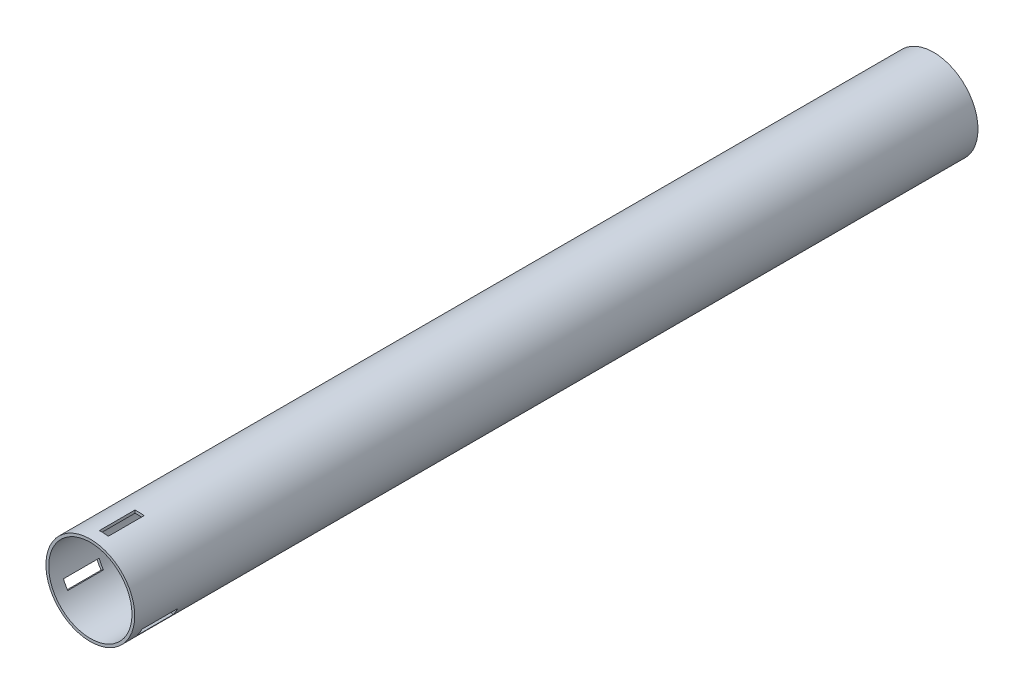
SolidWorks part; units mm, degrees
ref_plane "Front Plane" through (0, 0, 0) normal (0, 0, 1) x (1, 0, 0)
ref_plane "Top Plane" through (0, 0, 0) normal (0, 1, 0) x (1, 0, 0)
ref_plane "Right Plane" through (0, 0, 0) normal (1, 0, 0) x (0, 0, -1)
sketch "Sketch1" plane through (0, 0, 0) normal (0, 0, 1) x (1, 0, 0)
  circle A0 centre (0, 0) radius 23.6982
  circle A1 centre (0, 0) radius 22.225
extrude "Boss-Extrude1" add sketch "Sketch1" along normal blind 450
ref_plane "Plane1" through (0, 50.8, 0) normal (0, 1, 0) x (1, 0, 0)
sketch "Sketch3" plane through (0, 50.8, 0) normal (0, 1, 0) x (1, 0, 0)
  line L0 (-23.6982, -450) -> (23.6982, -450) construction
  line L2 (3.2689, -443.65) -> (3.2689, -424.6)
  line L3 (-1.5875, -443.65) -> (-1.5875, -424.6)
  line L4 (-1.5875, -424.6) -> (3.2689, -424.6)
  line L5 (-1.5875, -443.65) -> (3.2689, -443.65)
  point P2 (3.2689, -381.4159)
  dimension "D1" = 6.35
  dimension "D2" = 19.05
extrude "Cut-Extrude2" cut sketch "Sketch3" against normal up to next and the other way through all
pattern_circular "CirPattern4" count 3 over 360 about axis through (0, 0, 0) along (0, 0, 1) of "Cut-Extrude2"
